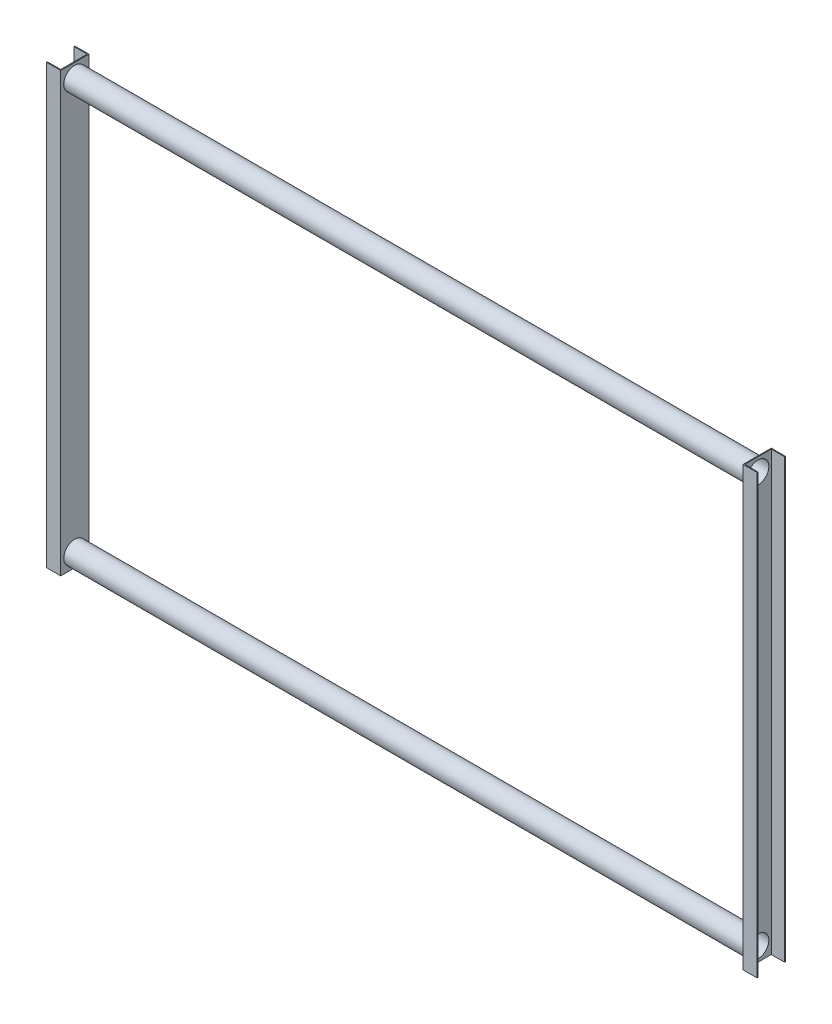
SolidWorks part; units mm, degrees
ref_plane "Front Plane" through (0, 0, 0) normal (0, 0, 1) x (1, 0, 0)
ref_plane "Top Plane" through (0, 0, 0) normal (0, 1, 0) x (1, 0, 0)
ref_plane "Right Plane" through (0, 0, 0) normal (1, 0, 0) x (0, 0, -1)
sketch "Sketch3" plane through (0, 0, 0) normal (0, 1, 0) x (1, 0, 0)
  line L0 (0, 209.8812) -> (0, -209.8812) construction
  line L1 (-51.5, 51.5) -> (0, 51.5)
  line L2 (-209.8812, 0) -> (209.8812, 0) construction
  line L3 (0, 51.5) -> (0, -51.5)
  line L4 (0, -51.5) -> (-51.5, -51.5)
  line L5 (-51.5, -51.5) -> (-51.5, -48.5)
  line L6 (-51.5, -48.5) -> (-3, -48.5)
  line L7 (-3, -48.5) -> (-3, 48.5)
  line L8 (-3, 48.5) -> (-51.5, 48.5)
  line L9 (-51.5, 48.5) -> (-51.5, 51.5)
  line L10 (2494, 209.8812) -> (2494, -209.8812) construction
  line L11 (1247, 209.8812) -> (1247, -209.8812) construction
  line L12 (2497, 48.5) -> (2545.5, 48.5)
  line L13 (2497, -48.5) -> (2497, 48.5)
  line L14 (2545.5, -48.5) -> (2497, -48.5)
  line L15 (2545.5, -51.5) -> (2545.5, -48.5)
  line L16 (2494, -51.5) -> (2545.5, -51.5)
  line L17 (2494, 51.5) -> (2494, -51.5)
  line L18 (2545.5, 51.5) -> (2494, 51.5)
  line L19 (2545.5, 48.5) -> (2545.5, 51.5)
  point P3 (0, 0)
  point P6 (0, 0)
  point P15 (0, 0)
  dimension "D1" = 103
  dimension "D2" = 3
  dimension "D3" = 3
  dimension "D4" = 3
  dimension "D5" = 51.5
  dimension "D6" = 51.5
  dimension "D7" = 2494
  dimension "D8" = 1247
extrude "Boss-Extrude1" add sketch "Sketch3" along normal blind 1600
sketch "Sketch7" plane through (-3, 0, 0) normal (-1, 0, 0) x (0, 0, 1)
  circle A0 centre (0, 50) radius 39.5
  circle A1 centre (0, 1550) radius 39.5
  point P2 (0, 0)
  point P6 (0, 0)
  point P7 (0, 0)
  dimension "D1" = 79
  dimension "D3" = 79
  dimension "D2" = 50
  dimension "D4" = 1500
extrude "Cut-Extrude2" cut sketch "Sketch7" against normal through all
sketch "Sketch8" plane through (0, 0, 0) normal (1, 0, 0) x (0, 0, -1)
  circle A0 centre (0, 50) radius 40.5
  circle A1 centre (0, 50) radius 39.5
  circle A2 centre (0, 1550) radius 40.5
  circle A3 centre (0, 1550) radius 39.5
  dimension "D1" = 81
  dimension "D3" = 81
  dimension "D2" = 1
  dimension "D4" = 1
extrude "Boss-Extrude2" add sketch "Sketch8" along normal up to surface (2494 mm away) up to face at (2494, 50, -39.5)
